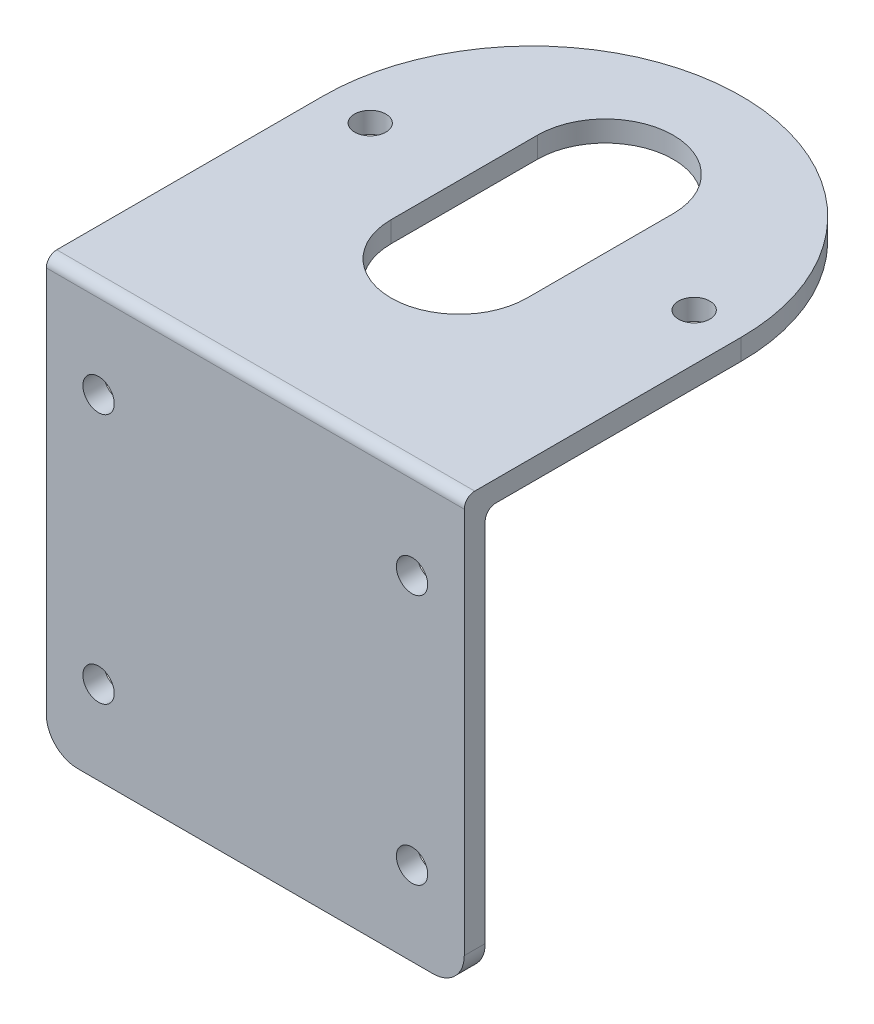
SolidWorks part; units mm, degrees
ref_plane "前视基准面" through (0, 0, 0) normal (0, 0, 1) x (1, 0, 0)
ref_plane "上视基准面" through (0, 0, 0) normal (0, 1, 0) x (1, 0, 0)
ref_plane "右视基准面" through (0, 0, 0) normal (1, 0, 0) x (0, 0, -1)
sketch "草图1" plane through (0, 0, 0) normal (0, 0, 1) x (1, 0, 0)
  line L0 (-20, 20.5) -> (20, 20.5)
  line L1 (20, -20.5) -> (-20, -20.5)
  line L2 (20, -20.5) -> (20, 20.5)
  line L3 (20, 20.5) -> (-20, 20.5)
  line L4 (-20, -20.5) -> (-20, 20.5)
  line L5 (20, -20.5) -> (-20, 20.5) construction
  line L6 (20, 20.5) -> (-20, -20.5) construction
  line L7 (-20, 20.5) -> (-20, 18.5)
  line L8 (20, 20.5) -> (20, 18.5)
  line L9 (-20, 18.5) -> (20, 18.5)
  circle A0 centre (-15, 11.5) radius 1.5
  circle A1 centre (-15, -12.5) radius 1.5
  circle A2 centre (15, -12.5) radius 1.5
  circle A3 centre (15, 11.5) radius 1.5
  point P0 (0, 0)
  dimension "D3" = 3
  dimension "D4" = 3
  dimension "D5" = 3
  dimension "D6" = 3
  dimension "D1" = 41
  dimension "D2" = 40
  dimension "D7" = 24
  dimension "D8" = 8
  dimension "D9" = 8
  dimension "D10" = 30
  dimension "D11" = 24
  dimension "D12" = 15
  dimension "D13" = 15
  dimension "D14" = 15
  dimension "D15" = 15
  dimension "D16" = 2
extrude "凸台-拉伸2" add sketch "草图1" along normal blind 2 contours L9 L4 L1 L2 A3 A2 A1 A0 | L4 L9 L2 L0
ref_plane "基准面4" through (0, 18.5, 0) normal (0, 1, 0) x (1, 0, 0)
sketch "草图2" plane through (0, 18.5, 0) normal (0, 1, 0) x (1, 0, 0)
  line L0 (-20, -2) -> (-20, 0) construction
  line L1 (-20, -2) -> (20, -2)
  line L2 (-20, -2) -> (-20, 24.5)
  line L3 (-20, 24.5) -> (20, 24.5)
  line L4 (20, -2) -> (20, 24.5)
  line L5 (20, -2) -> (20, 0) construction
  line L6 (-20, -2) -> (20, -2) construction
  line L7 (0, 31.5) -> (0, 17.5) construction
  line L8 (6.5, 31.5) -> (6.5, 17.5)
  line L9 (-6.5, 31.5) -> (-6.5, 17.5)
  circle A0 centre (0, 24.5) radius 20
  circle A1 centre (0, 24.5) radius 15.5 construction
  arc A2 (6.5, 31.5) -> (-6.5, 31.5) centre (0, 31.5) ccw
  arc A3 (-6.5, 17.5) -> (6.5, 17.5) centre (0, 17.5) ccw
  circle A4 centre (-15.5, 24.5) radius 1.5
  circle A5 centre (15.5, 24.5) radius 1.5018
  point P8 (20, -1)
  point P18 (0, 24.5)
  dimension "D4" = 31
  dimension "D7" = 6.5
  dimension "D9" = 6.5
  dimension "D10" = 3.0035
  dimension "D11" = 3
  dimension "D1" = 0
  dimension "D2" = 0
  dimension "D3" = 26.5
  dimension "D5" = 0
  dimension "D6" = 14
  dimension "D8" = 6.5
extrude "凸台-拉伸3" add sketch "草图2" along normal blind 2 contours A5 L3 A0 A4 L9 A2 L8 | A5 L3 L8 A3 L9 A4 A0 | A0 L2 L1 L4
fillet "圆角1" radius 1 2 edges at (0, 18.5, 0) (0, 20.5, 2)
fillet "圆角2" radius 3 2 edges at (-20, -20.5, 1) (20, -20.5, 1)
